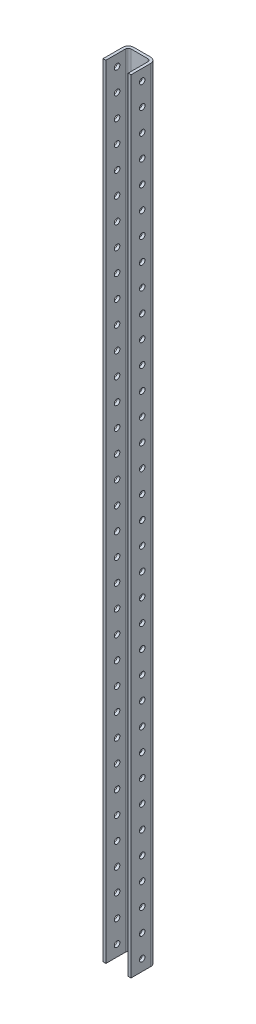
SolidWorks part; units mm, degrees
material "5052-O"
ref_plane "Front Plane" through (0, 0, 0) normal (0, 0, 1) x (1, 0, 0)
ref_plane "Top Plane" through (0, 0, 0) normal (0, 1, 0) x (1, 0, 0)
ref_plane "Rithe Plane" through (0, 0, 0) normal (1, 0, 0) x (0, 0, -1)
sketch "Sketch1" plane through (0, 0, 0) normal (0, 1, 0) x (1, 0, 0)
  line L0 (0, 103.632) -> (0, -110.3752) construction
  line L1 (-12.7, 0) -> (-12.7, 22.225)
  line L2 (-9.525, 25.4) -> (9.525, 25.4)
  line L3 (12.7, 22.225) -> (12.7, 0)
  line L4 (12.7, 0) -> (15.875, 0)
  line L5 (15.875, 0) -> (15.875, 22.225)
  line L6 (9.525, 28.575) -> (-9.525, 28.575)
  line L7 (-15.875, 22.225) -> (-15.875, 0)
  line L8 (-15.875, 0) -> (-12.7, 0)
  arc A0 (-12.7, 22.225) -> (-9.525, 25.4) centre (-9.525, 22.225) cw
  arc A1 (12.7, 22.225) -> (9.525, 25.4) centre (9.525, 22.225) ccw
  arc A2 (9.525, 28.575) -> (15.875, 22.225) centre (9.525, 22.225) cw
  arc A3 (-15.875, 22.225) -> (-9.525, 28.575) centre (-9.525, 22.225) cw
  dimension "D5" = 3.175
  dimension "D6" = 6.35
  dimension "D1" = 31.75
  dimension "D2" = 25.4
  dimension "D3" = 28.575
  dimension "D4" = 25.4
extrude "Extrude1" add sketch "Sketch1" along normal mid plane 889
sketch "Sketch2" plane through (0, 0, -28.575) normal (0, 0, -1) x (-1, 0, 0)
  line L0 (0, 461.5657) -> (0, -466.4615) construction
  line L1 (-9.525, 444.5) -> (9.525, 444.5) construction
  line L2 (-9.525, -444.5) -> (9.525, -444.5) construction
  circle A0 centre (0, 444.5) radius 1.59 construction
  circle A1 centre (1.905, 361.95) radius 4.826
  circle A2 centre (1.905, 336.55) radius 4.826
  circle A3 centre (1.905, 107.95) radius 4.826
  circle A4 centre (1.905, 82.55) radius 4.826
  circle A5 centre (-1.905, 0) radius 4.826
  circle A6 centre (1.905, -361.95) radius 4.826
  circle A7 centre (1.905, -336.55) radius 4.826
  circle A8 centre (1.905, -82.55) radius 4.826
  circle A9 centre (1.905, -107.95) radius 4.826
  circle A10 centre (0, -241.3) radius 1.5875
  dimension "D1" = 3.18
  dimension "D2" = 3.175
  dimension "D6" = 9.652
  dimension "D11" = 9.652
  dimension "D14" = 95.25
  dimension "D3" = 1.905
  dimension "D4" = 82.55
  dimension "D5" = 25.4
  dimension "D7" = 25.4
  dimension "D8" = 254
  dimension "D9" = 1.905
  dimension "D10" = 444.5
  dimension "D12" = 82.55
  dimension "D13" = 25.4
  dimension "D15" = 25.4
  dimension "D16" = 228.6
extrude "Extrude2" cut sketch "Sketch2" against normal blind 25
sketch "Sketch3" plane through (15.875, 0, 0) normal (1, 0, 0) x (0, 0, -1)
  line L1 (28.575, 444.5) -> (28.575, -444.5) construction
  circle A0 centre (12.7, 431.8) radius 3.175
  circle A1 centre (12.7, 406.4) radius 3.175
  circle A2 centre (12.7, 381) radius 3.175
  circle A3 centre (12.7, 355.6) radius 3.175
  circle A4 centre (12.7, 330.2) radius 3.175
  circle A5 centre (12.7, 304.8) radius 3.175
  circle A6 centre (12.7, 279.4) radius 3.175
  circle A7 centre (12.7, 254) radius 3.175
  circle A8 centre (12.7, 228.6) radius 3.175
  circle A9 centre (12.7, 203.2) radius 3.175
  circle A10 centre (12.7, 177.8) radius 3.175
  circle A11 centre (12.7, 152.4) radius 3.175
  circle A12 centre (12.7, 127) radius 3.175
  circle A13 centre (12.7, 101.6) radius 3.175
  circle A14 centre (12.7, 76.2) radius 3.175
  circle A15 centre (12.7, 50.8) radius 3.175
  circle A16 centre (12.7, 25.4) radius 3.175
  circle A17 centre (12.7, 0) radius 3.175
  circle A18 centre (12.7, -25.4) radius 3.175
  circle A19 centre (12.7, -50.8) radius 3.175
  circle A20 centre (12.7, -76.2) radius 3.175
  circle A21 centre (12.7, -101.6) radius 3.175
  circle A22 centre (12.7, -127) radius 3.175
  circle A23 centre (12.7, -152.4) radius 3.175
  circle A24 centre (12.7, -177.8) radius 3.175
  circle A25 centre (12.7, -203.2) radius 3.175
  circle A26 centre (12.7, -228.6) radius 3.175
  circle A27 centre (12.7, -254) radius 3.175
  circle A28 centre (12.7, -279.4) radius 3.175
  circle A29 centre (12.7, -304.8) radius 3.175
  circle A30 centre (12.7, -330.2) radius 3.175
  circle A31 centre (12.7, -355.6) radius 3.175
  circle A32 centre (12.7, -381) radius 3.175
  circle A33 centre (12.7, -406.4) radius 3.175
  circle A34 centre (12.7, -431.8) radius 3.175
  dimension "D1" = 6.35
  dimension "D2" = 12.7
  dimension "D3" = 15.875
  dimension "D4" = 25.4
extrude "Extrude3" cut sketch "Sketch3" against normal blind 35
